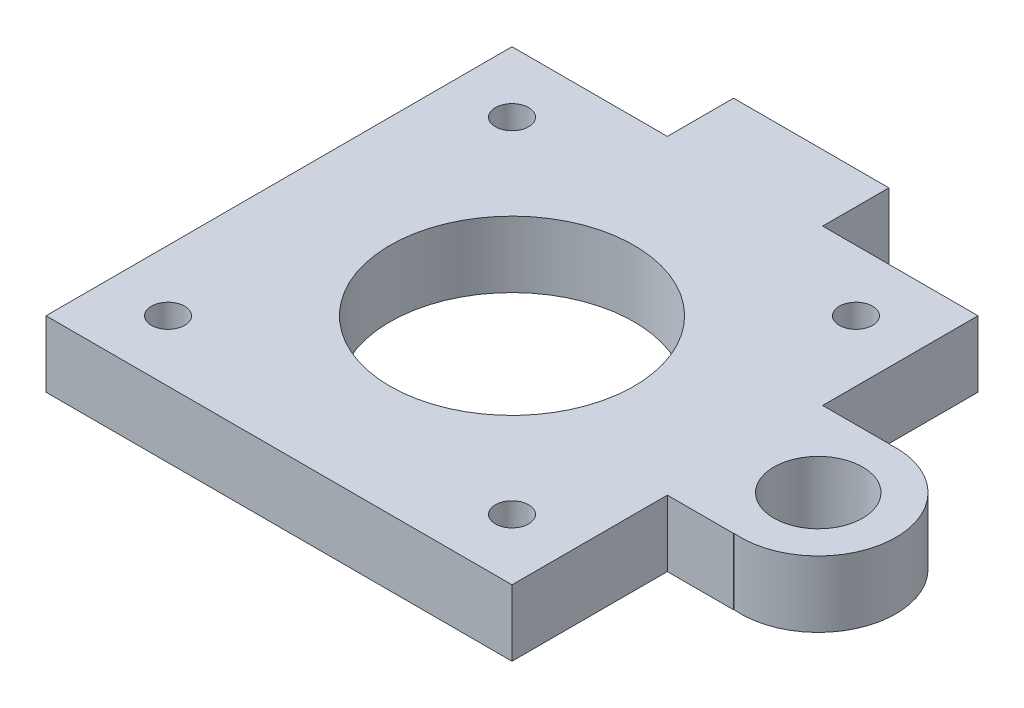
SolidWorks part; units mm, degrees
ref_plane "Front Plane" through (0, 0, 0) normal (0, 0, 1) x (1, 0, 0)
ref_plane "Top Plane" through (0, 0, 0) normal (0, 1, 0) x (1, 0, 0)
ref_plane "Right Plane" through (0, 0, 0) normal (1, 0, 0) x (0, 0, -1)
sketch "Sketch1" plane through (0, 0, 0) normal (0, 1, 0) x (1, 0, 0)
  line L0 (0, 21) -> (42, 21) construction
  line L1 (0, 0) -> (42, 0)
  line L2 (0, 0) -> (0, 42)
  line L3 (0, 42) -> (42, 42)
  line L4 (42, 0) -> (42, 42)
  line L5 (21, 42) -> (21, 0) construction
  line L6 (5.5, 36.5) -> (0, 36.5) construction
  line L7 (5.5, 36.5) -> (5.5, 42) construction
  line L8 (36.5, 5.5) -> (42, 5.5) construction
  line L9 (36.5, 5.5) -> (36.5, 0) construction
  circle A0 centre (21, 21) radius 11
  circle A1 centre (5.5, 36.5) radius 1.5
  circle A2 centre (36.5, 36.5) radius 1.5
  circle A3 centre (36.5, 5.5) radius 1.5
  circle A4 centre (5.5, 5.5) radius 1.5
  dimension "D2" = 22
  dimension "D4" = 3
  dimension "D1" = 42
  dimension "D3" = 31
extrude "Boss-Extrude1" add sketch "Sketch1" along normal blind 5.969
sketch "Sketch2" plane through (0, 5.969, 0) normal (0, 1, 0) x (1, 0, 0)
  line L0 (0, 42) -> (14, 42) construction
  line L1 (42, 42) -> (0, 42) construction
  line L2 (14, 42) -> (14, 47.969)
  line L3 (14, 47.969) -> (28, 47.969)
  line L4 (28, 47.969) -> (28, 42)
  line L5 (28, 42) -> (42, 42) construction
  line L6 (14, 42) -> (28, 42)
  line L7 (42, 0) -> (42, 42) construction
  line L8 (42, 28) -> (47.969, 28)
  line L9 (42, 28) -> (42, 14)
  line L10 (42, 14) -> (47.969, 14)
  line L11 (47.969, 28) -> (47.969, 14)
  line L14 (42, 42) -> (42, 28) construction
  line L15 (42, 0) -> (42, 14) construction
  dimension "D1" = 5.969
  dimension "D2" = 5.969
extrude "Boss-Extrude2" add sketch "Sketch2" along direction (0, -1, 0) on the side against the normal blind 5.969
sketch "Sketch4" plane through (0, 5.969, 0) normal (0, 1, 0) x (1, 0, 0)
  line L0 (0, 21) -> (47.969, 21) construction
  line L1 (0, 42) -> (0, 0) construction
  line L2 (47.969, 14) -> (47.969, 28) construction
  line L3 (21, 47.969) -> (21, 0) construction
  line L4 (28, 47.969) -> (14, 47.969) construction
  line L5 (0, 0) -> (42, 0) construction
  line L6 (21, 21) -> (48.6039, 21) construction
  circle A0 centre (48.6039, 21) radius 7
  dimension "D2" = 14
  dimension "D1" = 27.6039
extrude "Boss-Extrude5" add sketch "Sketch4" against normal blind 5.969
sketch "Sketch6" plane through (0, 5.969, 0) normal (0, 1, 0) x (1, 0, 0)
  line L0 (21, 47.969) -> (21, 0) construction
  line L1 (28, 47.969) -> (14, 47.969) construction
  line L2 (0, 0) -> (42, 0) construction
  line L3 (0, 21) -> (55.6039, 21) construction
  line L4 (0, 42) -> (0, 0) construction
  line L5 (21, 21) -> (48.6039, 21) construction
  arc A0 (47.969, 14.0289) -> (47.969, 27.9711) centre (48.6039, 21) ccw construction
  circle A1 centre (48.6039, 21) radius 4
  dimension "D2" = 8
  dimension "D1" = 27.6039
extrude "Cut-Extrude2" cut sketch "Sketch6" against normal blind 6.35
